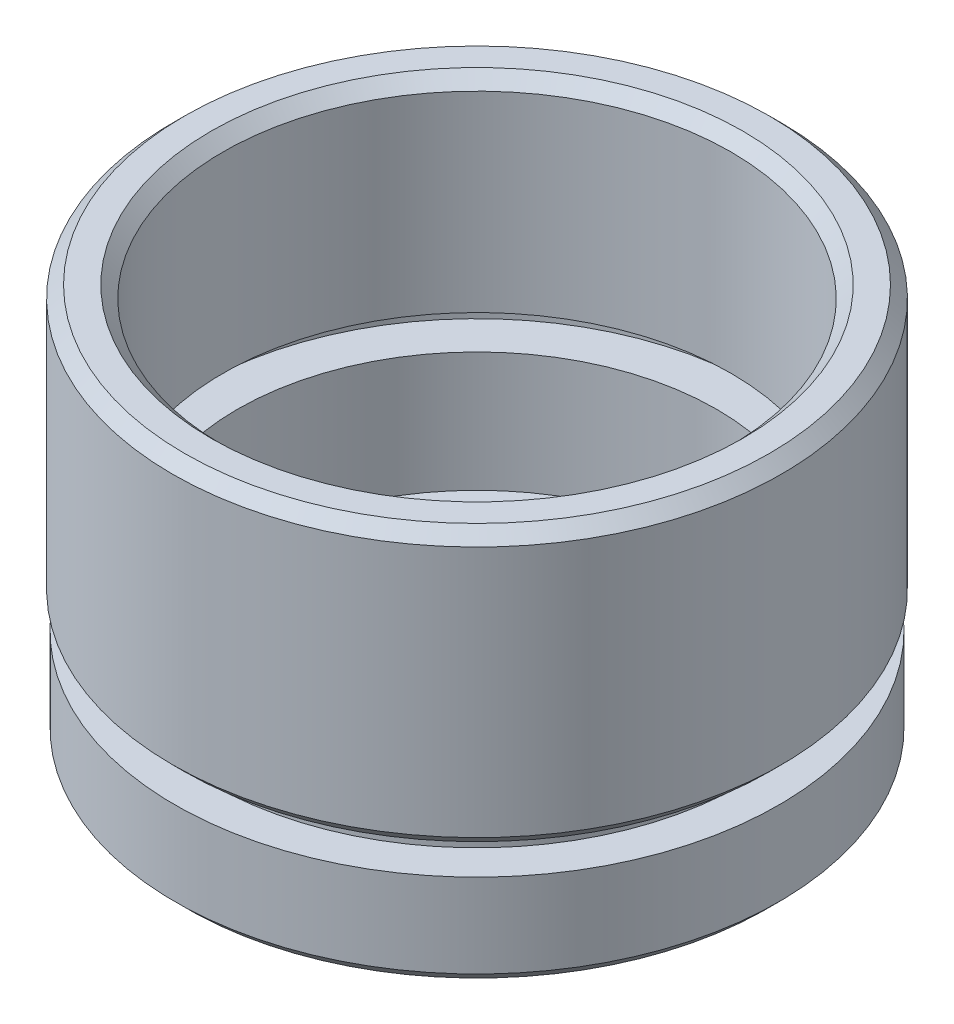
SolidWorks part; units mm, degrees
ref_plane "前视基准面" through (0, 0, 0) normal (0, 0, 1) x (1, 0, 0)
ref_plane "上视基准面" through (0, 0, 0) normal (0, 1, 0) x (1, 0, 0)
ref_plane "右视基准面" through (0, 0, 0) normal (1, 0, 0) x (0, 0, -1)
sketch "草图1" plane through (0, 0, 0) normal (0, 0, 1) x (1, 0, 0)
  line L0 (0, 0) -> (0, 21.8535) construction
  line L1 (9.25, 0) -> (12.6, 0)
  line L2 (12.6, 0) -> (12.6, 4)
  line L3 (12.6, 4) -> (11.1, 4)
  line L4 (11.1, 4) -> (11.1, 5)
  line L5 (11.1, 5) -> (12.7, 5)
  line L6 (12.7, 5) -> (12.7, 16.5)
  line L7 (12.7, 16.5) -> (10.6, 16.5)
  line L8 (10.6, 16.5) -> (10.6, 8)
  line L9 (10.6, 8) -> (11.7, 8)
  line L10 (11.7, 8) -> (11.7, 7)
  line L11 (11.7, 7) -> (10, 7)
  line L12 (10, 7) -> (10, 2)
  line L13 (10, 2) -> (9.25, 2)
  line L14 (9.25, 0) -> (9.25, 2)
  dimension "D1" = 16.5
  dimension "D2" = 12.7
  dimension "D3" = 10.6
  dimension "D4" = 10
  dimension "D5" = 1
  dimension "D6" = 5
  dimension "D7" = 9.25
  dimension "D8" = 12.6
  dimension "D9" = 1
  dimension "D10" = 5
  dimension "D11" = 2
  dimension "D12" = 11.7
  dimension "D13" = 11.1
revolve "旋转1" add sketch "草图1" angle 360 about L0
cosmetic thread "装饰螺纹线11"
cosmetic thread "装饰螺纹线12"
chamfer "倒角1" distance 0.5 angle 45 4 edges at (0, 16.5, -10.6) (0, 16.5, -12.7) (0, 5, -12.7) (0, 0, -12.6)
